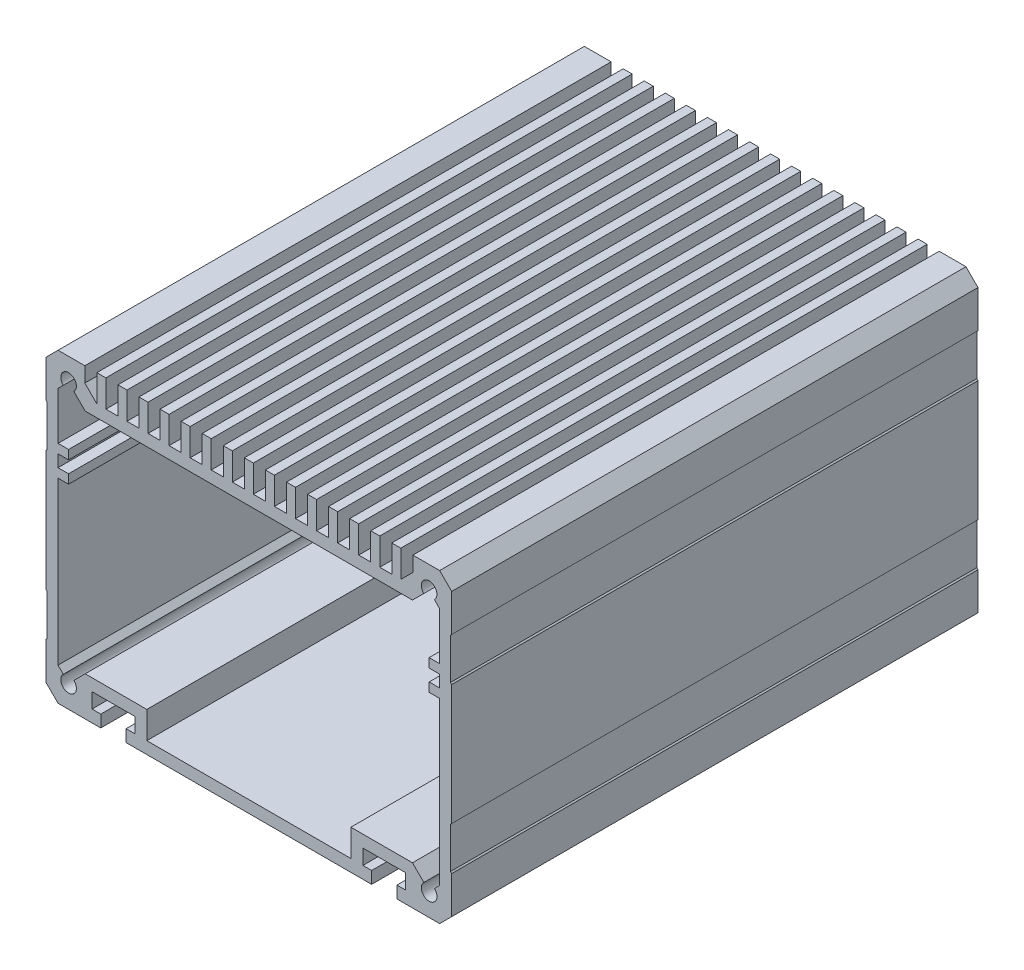
SolidWorks part; units mm, degrees
ref_plane "Front Plane" through (0, 0, 0) normal (0, 0, 1) x (1, 0, 0)
ref_plane "Top Plane" through (0, 0, 0) normal (0, 1, 0) x (1, 0, 0)
ref_plane "Right Plane" through (0, 0, 0) normal (1, 0, 0) x (0, 0, -1)
sketch "Sketch1" plane through (0, 0, 12.5605) normal (0, 0, 1) x (1, 0, 0)
  line L0 (-33.7882, -0.1924) -> (-33.7882, 50.6076) construction
  line L1 (-56.2882, -0.1924) -> (-56.2882, 4.3076) construction
  line L2 (-54.1882, 1.8076) -> (-54.1882, -0.1924)
  line L3 (-52.7382, 1.8076) -> (-54.1882, 1.8076)
  line L4 (-52.7382, 4.3076) -> (-52.7382, 1.8076)
  line L5 (-59.8382, 4.3076) -> (-52.7382, 4.3076)
  line L6 (-59.8382, 1.8076) -> (-59.8382, 4.3076)
  line L7 (-58.3882, 1.8076) -> (-59.8382, 1.8076)
  line L8 (-58.3882, -0.1924) -> (-58.3882, 1.8076)
  line L9 (-65.4882, -0.1924) -> (-58.3882, -0.1924)
  line L10 (-67.4882, 1.8076) -> (-65.4882, -0.1924)
  line L11 (-67.4882, 8.0076) -> (-67.4882, 1.8076)
  line L12 (-67.2882, 8.2076) -> (-67.4882, 8.0076)
  line L13 (-67.2882, 15.0076) -> (-67.2882, 8.2076)
  line L14 (-67.4882, 15.2076) -> (-67.2882, 15.0076)
  line L15 (-67.4882, 35.2076) -> (-67.4882, 15.2076)
  line L16 (-67.2882, 35.4076) -> (-67.4882, 35.2076)
  line L17 (-67.2882, 42.2076) -> (-67.2882, 35.4076)
  line L18 (-67.4882, 42.4076) -> (-67.2882, 42.2076)
  line L19 (-67.4882, 48.6076) -> (-67.4882, 42.4076)
  line L20 (-65.4882, 50.6076) -> (-67.4882, 48.6076)
  line L21 (-61.0382, 50.6076) -> (-65.4882, 50.6076)
  line L22 (-61.0382, 48.1076) -> (-61.0382, 50.6076)
  line L23 (-2.0882, 32.2076) -> (-2.0882, 5.294)
  line L24 (-2.0882, 5.294) -> (-2.9632, 4.419)
  line L25 (-4.7132, 4.419) -> (-6.6018, 6.3076)
  line L26 (-11.2882, -0.1924) -> (-11.2882, 4.3076) construction
  line L27 (-59.0382, 46.1076) -> (-61.0382, 48.1076)
  line L28 (-59.0382, 50.6076) -> (-59.0382, 46.1076)
  line L29 (-57.5382, 50.6076) -> (-59.0382, 50.6076)
  line L30 (-57.5382, 46.1076) -> (-57.5382, 50.6076)
  line L31 (-55.5382, 46.1076) -> (-57.5382, 46.1076)
  line L32 (-55.5382, 50.6076) -> (-55.5382, 46.1076)
  line L33 (-54.0382, 50.6076) -> (-55.5382, 50.6076)
  line L34 (-6.6018, 6.3076) -> (-16.8382, 6.3076)
  line L35 (-16.8382, 6.3076) -> (-16.8382, 1.8076)
  line L36 (-16.8382, 1.8076) -> (-50.7382, 1.8076)
  line L37 (-54.0382, 46.1076) -> (-54.0382, 50.6076)
  line L38 (-52.0382, 46.1076) -> (-54.0382, 46.1076)
  line L39 (-52.0382, 50.6076) -> (-52.0382, 46.1076)
  line L40 (-50.5382, 50.6076) -> (-52.0382, 50.6076)
  line L41 (-50.5382, 46.1076) -> (-50.5382, 50.6076)
  line L42 (-48.5382, 46.1076) -> (-50.5382, 46.1076)
  line L43 (-48.5382, 50.6076) -> (-48.5382, 46.1076)
  line L44 (-47.0382, 50.6076) -> (-48.5382, 50.6076)
  line L45 (-47.0382, 46.1076) -> (-47.0382, 50.6076)
  line L46 (-45.0382, 46.1076) -> (-47.0382, 46.1076)
  line L47 (-45.0382, 50.6076) -> (-45.0382, 46.1076)
  line L48 (-43.5382, 50.6076) -> (-45.0382, 50.6076)
  line L49 (-43.5382, 46.1076) -> (-43.5382, 50.6076)
  line L50 (-41.5382, 46.1076) -> (-43.5382, 46.1076)
  line L51 (-41.5382, 50.6076) -> (-41.5382, 46.1076)
  line L52 (-40.0382, 50.6076) -> (-41.5382, 50.6076)
  line L53 (-40.0382, 46.1076) -> (-40.0382, 50.6076)
  line L54 (-38.0382, 46.1076) -> (-40.0382, 46.1076)
  line L55 (-38.0382, 50.6076) -> (-38.0382, 46.1076)
  line L56 (-36.5382, 50.6076) -> (-38.0382, 50.6076)
  line L57 (-36.5382, 46.1076) -> (-36.5382, 50.6076)
  line L58 (-34.5382, 46.1076) -> (-36.5382, 46.1076)
  line L59 (-34.5382, 50.6076) -> (-34.5382, 46.1076)
  line L60 (-63.7382, 32.2076) -> (-65.4882, 32.2076)
  line L61 (-63.7382, 33.7076) -> (-63.7382, 32.2076)
  line L62 (-65.4882, 33.7076) -> (-63.7382, 33.7076)
  line L63 (-65.4882, 35.7076) -> (-65.4882, 33.7076)
  line L64 (-63.7382, 35.7076) -> (-65.4882, 35.7076)
  line L65 (-63.7382, 37.2076) -> (-63.7382, 35.7076)
  line L66 (-65.4882, 37.2076) -> (-63.7382, 37.2076)
  line L67 (-65.4882, 45.1211) -> (-65.4882, 37.2076)
  line L68 (-64.6132, 45.9961) -> (-65.4882, 45.1211)
  line L69 (-60.9747, 44.1076) -> (-62.8632, 45.9961)
  line L70 (-50.7382, 6.3076) -> (-50.7382, 1.8076)
  line L71 (-60.9747, 6.3076) -> (-50.7382, 6.3076)
  line L72 (-62.8632, 4.419) -> (-60.9747, 6.3076)
  line L73 (-65.4882, 5.294) -> (-64.6132, 4.419)
  line L74 (-65.4882, 32.2076) -> (-65.4882, 5.294)
  line L75 (-0.0882, 25.2076) -> (-33.7882, 25.2076) construction
  line L104 (-60.9747, 44.1076) -> (-6.6018, 44.1076)
  line L105 (-6.6018, 44.1076) -> (-4.7132, 45.9961)
  line L106 (-2.9632, 45.9961) -> (-2.0882, 45.1211)
  line L107 (-2.0882, 45.1211) -> (-2.0882, 37.2076)
  line L116 (-2.0882, 37.2076) -> (-3.8382, 37.2076)
  line L117 (-3.8382, 37.2076) -> (-3.8382, 35.7076)
  line L118 (-3.8382, 35.7076) -> (-2.0882, 35.7076)
  line L119 (-2.0882, 35.7076) -> (-2.0882, 33.7076)
  line L120 (-2.0882, 33.7076) -> (-3.8382, 33.7076)
  line L121 (-3.8382, 33.7076) -> (-3.8382, 32.2076)
  line L122 (-3.8382, 32.2076) -> (-2.0882, 32.2076)
  line L145 (-34.5382, 50.6076) -> (-33.0382, 50.6076)
  line L146 (-33.0382, 50.6076) -> (-33.0382, 46.1076)
  line L147 (-33.0382, 46.1076) -> (-31.0382, 46.1076)
  line L148 (-31.0382, 46.1076) -> (-31.0382, 50.6076)
  line L149 (-31.0382, 50.6076) -> (-29.5382, 50.6076)
  line L150 (-29.5382, 50.6076) -> (-29.5382, 46.1076)
  line L151 (-29.5382, 46.1076) -> (-27.5382, 46.1076)
  line L152 (-27.5382, 46.1076) -> (-27.5382, 50.6076)
  line L153 (-27.5382, 50.6076) -> (-26.0382, 50.6076)
  line L154 (-26.0382, 50.6076) -> (-26.0382, 46.1076)
  line L155 (-26.0382, 46.1076) -> (-24.0382, 46.1076)
  line L156 (-24.0382, 46.1076) -> (-24.0382, 50.6076)
  line L157 (-24.0382, 50.6076) -> (-22.5382, 50.6076)
  line L158 (-22.5382, 50.6076) -> (-22.5382, 46.1076)
  line L159 (-22.5382, 46.1076) -> (-20.5382, 46.1076)
  line L160 (-20.5382, 46.1076) -> (-20.5382, 50.6076)
  line L161 (-20.5382, 50.6076) -> (-19.0382, 50.6076)
  line L162 (-19.0382, 50.6076) -> (-19.0382, 46.1076)
  line L163 (-19.0382, 46.1076) -> (-17.0382, 46.1076)
  line L164 (-17.0382, 46.1076) -> (-17.0382, 50.6076)
  line L165 (-17.0382, 50.6076) -> (-15.5382, 50.6076)
  line L166 (-15.5382, 50.6076) -> (-15.5382, 46.1076)
  line L167 (-15.5382, 46.1076) -> (-13.5382, 46.1076)
  line L168 (-13.5382, 46.1076) -> (-13.5382, 50.6076)
  line L169 (-13.5382, 50.6076) -> (-12.0382, 50.6076)
  line L170 (-12.0382, 50.6076) -> (-12.0382, 46.1076)
  line L171 (-12.0382, 46.1076) -> (-10.0382, 46.1076)
  line L172 (-10.0382, 46.1076) -> (-10.0382, 50.6076)
  line L173 (-10.0382, 50.6076) -> (-8.5382, 50.6076)
  line L174 (-8.5382, 50.6076) -> (-8.5382, 46.1076)
  line L175 (-8.5382, 46.1076) -> (-6.5382, 48.1076)
  line L176 (-6.5382, 48.1076) -> (-6.5382, 50.6076)
  line L177 (-6.5382, 50.6076) -> (-2.0882, 50.6076)
  line L178 (-2.0882, 50.6076) -> (-0.0882, 48.6076)
  line L179 (-0.0882, 48.6076) -> (-0.0882, 42.4076)
  line L180 (-0.0882, 42.4076) -> (-0.2882, 42.2076)
  line L181 (-0.2882, 42.2076) -> (-0.2882, 35.4076)
  line L182 (-0.2882, 35.4076) -> (-0.0882, 35.2076)
  line L183 (-0.0882, 35.2076) -> (-0.0882, 15.2076)
  line L184 (-0.0882, 15.2076) -> (-0.2882, 15.0076)
  line L185 (-0.2882, 15.0076) -> (-0.2882, 8.2076)
  line L186 (-0.2882, 8.2076) -> (-0.0882, 8.0076)
  line L187 (-0.0882, 8.0076) -> (-0.0882, 1.8076)
  line L188 (-0.0882, 1.8076) -> (-2.0882, -0.1924)
  line L189 (-2.0882, -0.1924) -> (-9.1882, -0.1924)
  line L190 (-9.1882, -0.1924) -> (-9.1882, 1.8076)
  line L191 (-9.1882, 1.8076) -> (-7.7382, 1.8076)
  line L192 (-7.7382, 1.8076) -> (-7.7382, 4.3076)
  line L193 (-7.7382, 4.3076) -> (-14.8382, 4.3076)
  line L194 (-14.8382, 4.3076) -> (-14.8382, 1.8076)
  line L195 (-14.8382, 1.8076) -> (-13.3882, 1.8076)
  line L196 (-13.3882, 1.8076) -> (-13.3882, -0.1924)
  line L197 (-13.3882, -0.1924) -> (-54.1882, -0.1924)
  arc A0 (-4.7132, 4.419) -> (-2.9632, 4.419) centre (-3.8382, 3.4576) ccw
  arc A1 (-64.6132, 45.9961) -> (-62.8632, 45.9961) centre (-63.7382, 46.9576) cw
  arc A2 (-62.8632, 4.419) -> (-64.6132, 4.419) centre (-63.7382, 3.4576) cw
  arc A3 (-2.9632, 45.9961) -> (-4.7132, 45.9961) centre (-3.8382, 46.9576) ccw
  point P2 (-11.2882, 4.3076)
  point P84 (-33.7882, 44.1076)
  point P85 (-33.7882, 1.8076)
  point P88 (-33.7882, 44.1076)
  point P89 (-33.7882, 44.1076)
  dimension "D7" = 1.3
  dimension "D2" = 2
  dimension "D3" = 1.8
  dimension "D4" = 6.5
  dimension "D5" = 4.2
  dimension "D6" = 7.1
  dimension "D8" = 2.5
  dimension "D9" = 31.7
  dimension "D10" = 33.7
  dimension "D11" = 1.8
  dimension "D12" = 135
  dimension "D13" = 135
  dimension "D14" = 2
  dimension "D15" = 3.65
  dimension "D16" = 3.75
  dimension "D17" = 3.65
  dimension "D18" = 2.5
  dimension "D19" = 2
  dimension "D20" = 2
  dimension "D21" = 50.8
  dimension "D22" = 2
  dimension "D23" = 22.5
  dimension "D24" = 0.75
  dimension "D25" = 1.5
  dimension "D26" = 2
  dimension "D27" = 10.4
  dimension "D28" = 1.75
  dimension "D29" = 20
extrude "Boss-Extrude1" add sketch "Sketch1" along normal up to surface (87.4395 mm away)
